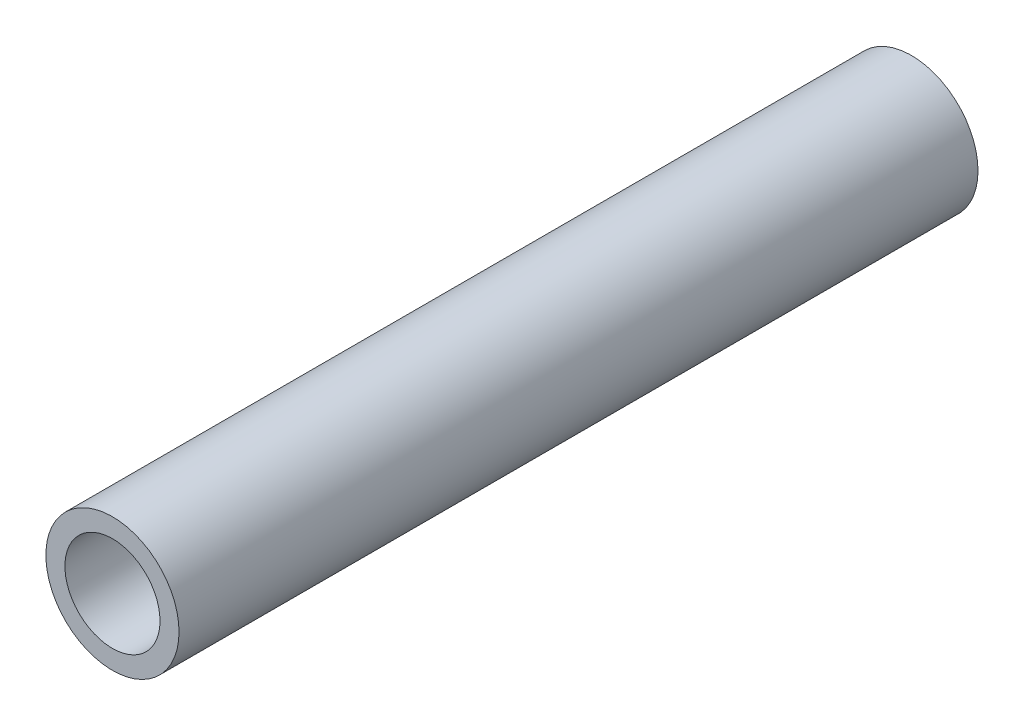
SolidWorks part; units mm, degrees
ref_plane "Front Plane" through (0, 0, 0) normal (0, 0, 1) x (1, 0, 0)
ref_plane "Top Plane" through (0, 0, 0) normal (0, 1, 0) x (1, 0, 0)
ref_plane "Right Plane" through (0, 0, 0) normal (1, 0, 0) x (0, 0, -1)
sketch "Sketch1" plane through (0, 0, 0) normal (0, 0, 1) x (1, 0, 0)
  circle A0 centre (0, 0) radius 3.5
  circle A1 centre (0, 0) radius 2.5
  dimension "D1" = 7
  dimension "D2" = 5
extrude "Boss-Extrude1" add sketch "Sketch1" along normal blind 42
